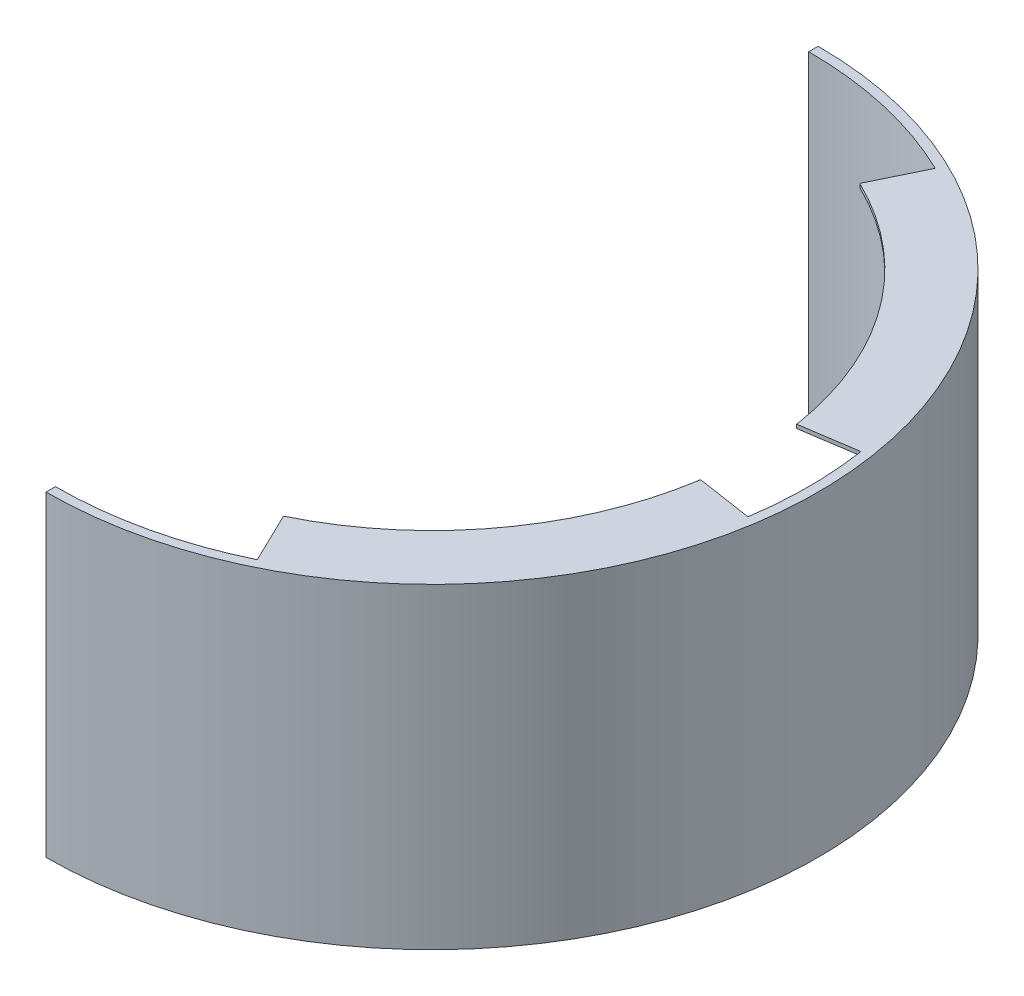
SolidWorks part; units mm, degrees
material "PLA"
ref_plane "Front Plane" through (0, 0, 0) normal (0, 0, 1) x (1, 0, 0)
ref_plane "Top Plane" through (0, 0, 0) normal (0, 1, 0) x (1, 0, 0)
ref_plane "Right Plane" through (0, 0, 0) normal (1, 0, 0) x (0, 0, -1)
sketch "Sketch1" plane through (0, 0, 0) normal (0, 1, 0) x (1, 0, 0)
  line L0 (0, 205) -> (0, 200)
  line L1 (0, -200) -> (0, -205)
  arc A0 (0, -205) -> (0, 205) centre (0, 0) ccw
  arc A1 (0, -200) -> (0, 200) centre (0, 0) ccw
  dimension "D1" = 410
  dimension "D2" = 400
extrude "Boss-Extrude1" add sketch "Sketch1" along normal blind 168
sketch "Sketch2" plane through (0, 0, 0) normal (0, 1, 0) x (1, 0, 0)
  line L0 (87.178, -180) -> (74.1013, -153)
  line L1 (197.7372, -30) -> (168.0766, -25.5)
  line L2 (197.7372, 30) -> (168.0766, 25.5)
  line L3 (87.178, 180) -> (74.1013, 153)
  line L4 (-194.4119, 0) -> (395.578, 0) construction
  arc A0 (74.1013, -153) -> (168.0766, -25.5) centre (0, 0) ccw
  arc A1 (0, -200) -> (0, 200) centre (0, 0) ccw construction
  arc A2 (87.178, -180) -> (197.7372, -30) centre (0, 0) ccw
  arc A3 (168.0766, 25.5) -> (74.1013, 153) centre (0, 0) ccw
  arc A4 (197.7372, 30) -> (87.178, 180) centre (0, 0) ccw
  dimension "D1" = 30
  dimension "D3" = 30
  dimension "D2" = 150
  dimension "D4" = 30
  dimension "D5" = 30
  dimension "D6" = 150
extrude "Boss-Extrude2" add sketch "Sketch2" along normal blind 2
ref_plane "Plane1" through (0, 84, 0) normal (0, 1, 0) x (1, 0, 0)
mirror "Mirror2" about plane through (0, 84, 0) normal (0, 1, 0) of "Boss-Extrude2"
